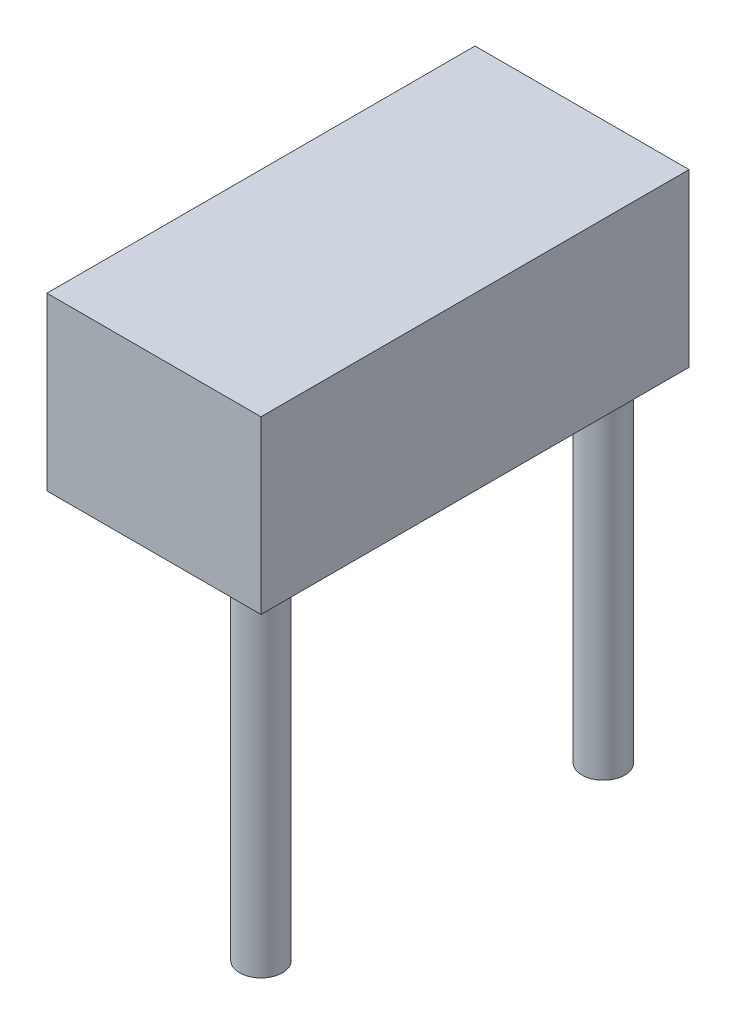
SolidWorks part; units mm, degrees
ref_plane "Front Plane" through (0, 0, 0) normal (0, 0, 1) x (1, 0, 0)
ref_plane "Top Plane" through (0, 0, 0) normal (0, 1, 0) x (1, 0, 0)
ref_plane "Right Plane" through (0, 0, 0) normal (1, 0, 0) x (0, 0, -1)
sketch "Sketch1" plane through (0, 0, 0) normal (0, 1, 0) x (1, 0, 0)
  line L1 (0, 0) -> (15.875, 0)
  line L2 (0, 0) -> (0, 31.75)
  line L3 (0, 31.75) -> (15.875, 31.75)
  line L4 (15.875, 0) -> (15.875, 31.75)
  dimension "D1" = 31.75
  dimension "D2" = 15.875
extrude "Boss-Extrude1" add sketch "Sketch1" along normal blind 12.7
sketch "Sketch2" plane through (0, 0, 0) normal (0, -1, 0) x (1, 0, 0)
  line L0 (12.7, 0) -> (12.7, -31.75) construction
  line L1 (0, 0) -> (15.875, 0) construction
  line L2 (15.875, -31.75) -> (0, -31.75) construction
  line L3 (15.875, 0) -> (15.875, -31.75) construction
  line L4 (12.7, -15.875) -> (0, -15.875) construction
  line L5 (0, -31.75) -> (0, 0) construction
  circle A0 centre (12.7, -3.175) radius 1.5875
  circle A1 centre (12.7, -28.575) radius 1.5875
  dimension "D2" = 3.175
  dimension "D3" = 3.175
  dimension "D1" = 3.175
extrude "Boss-Extrude2" add sketch "Sketch2" along normal blind 25.4
